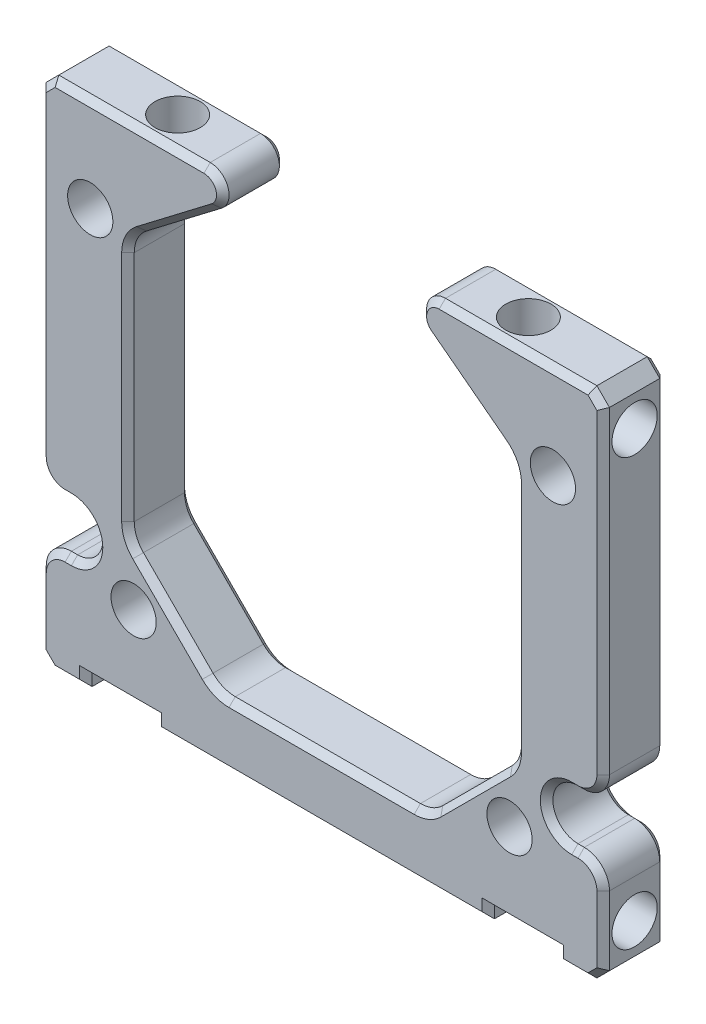
SolidWorks part; units mm, degrees
ref_plane "Front Plane" through (0, 0, 0) normal (0, 0, 1) x (1, 0, 0)
ref_plane "Top Plane" through (0, 0, 0) normal (0, 1, 0) x (1, 0, 0)
ref_plane "Right Plane" through (0, 0, 0) normal (1, 0, 0) x (0, 0, -1)
sketch "Sketch2" plane through (0, 0, 0) normal (0, 0, 1) x (1, 0, 0)
  line L0 (-22.4, 0) -> (22.4, 0) construction
  line L1 (-22.4, 20.4) -> (22.4, 20.4)
  line L2 (-22.4, 20.4) -> (-22.4, -20.4)
  line L3 (-22.4, -20.4) -> (22.4, -20.4)
  line L4 (22.4, 20.4) -> (22.4, -20.4)
  line L5 (0, 15.4) -> (0, -15.4) construction
  line L6 (-15.4, 15.4) -> (15.4, 15.4)
  line L7 (-15.4, 15.4) -> (-15.4, -15.4)
  line L8 (-15.4, -15.4) -> (15.4, -15.4)
  line L9 (15.4, 15.4) -> (15.4, -15.4)
  point P6 (0, 0)
  point P14 (0, 0)
  dimension "D1" = 44.8
  dimension "D2" = 40.8
  dimension "D3" = 5
  dimension "D4" = 7
extrude "Boss-Extrude1" add sketch "Sketch2" along normal blind 5
chamfer "Chamfer1" distance 1 angle 45 4 edges at (-22.4, -20.4, 2.5) (22.4, -20.4, 2.5) (22.4, 20.4, 2.5) (-22.4, 20.4, 2.5)
chamfer "Chamfer2" distance 7 angle 45 4 edges at (-15.4, -15.4, 2.5) (15.4, -15.4, 2.5) (15.4, 15.4, 2.5) (-15.4, 15.4, 2.5)
sketch "Sketch3" plane through (0, 0, 5) normal (0, 0, 1) x (1, 0, 0)
  line L0 (21.4, 20.4) -> (-21.4, 20.4) construction
  line L1 (22.4, -19.4) -> (22.4, 19.4) construction
  circle A0 centre (14.95, 12.95) radius 1.8
  dimension "D1" = 3.6
  dimension "D2" = 7.45
  dimension "D3" = 7.45
extrude "Cut-Extrude1" cut sketch "Sketch3" against normal through all
sketch "Sketch4" plane through (0, 20.4, 0) normal (0, 1, 0) x (1, 0, 0)
  line L0 (21.4, -5) -> (-21.4, -5) construction
  line L1 (22.4, 0) -> (22.4, -5) construction
  circle A0 centre (13.95, -2.5) radius 1.8
  dimension "D1" = 3.6
  dimension "D2" = 2.5
  dimension "D3" = 8.45
extrude "Cut-Extrude2" cut sketch "Sketch4" against normal blind 5
sketch "Sketch5" plane through (22.4, 0, 0) normal (1, 0, 0) x (0, 0, -1)
  line L0 (-5, -19.4) -> (-5, 19.4) construction
  line L1 (-5, 20.4) -> (0, 20.4) construction
  circle A0 centre (-2.5, 16.95) radius 1.8
  dimension "D2" = 3.6
  dimension "D3" = 3.45
  dimension "D1" = 2.5
extrude "Cut-Extrude3" cut sketch "Sketch5" against normal blind 5
mirror "Mirror1" about plane through (0, 0, 0) normal (0, 1, 0) of "Cut-Extrude3", "Cut-Extrude1"
mirror "Mirror2" about plane through (0, 0, 0) normal (1, 0, 0) of "Cut-Extrude2", "Mirror1", "Cut-Extrude1", "Cut-Extrude3"
sketch "Sketch8" plane through (0, 0, 5) normal (0, 0, 1) x (1, 0, 0)
  circle A0 centre (14.95, 12.95) radius 1.8
  circle A1 centre (-14.95, 12.95) radius 1.8
  circle A3 centre (-14.95, 12.95) radius 1.8 construction
  circle A4 centre (14.95, 12.95) radius 1.8 construction
extrude "Boss-Extrude2" add sketch "Sketch8" against normal up to surface (5 mm away) up to face at (16.75, -12.95, 0)
sketch "Sketch9" plane through (0, 0, 5) normal (0, 0, 1) x (1, 0, 0)
  line L0 (21.4, 20.4) -> (-21.4, 20.4) construction
  line L1 (22.4, -19.4) -> (22.4, 19.4) construction
  line L2 (-22.4, 19.4) -> (-22.4, -19.4) construction
  circle A0 centre (18.4, 12.95) radius 1.8
  circle A1 centre (-18.4, 12.95) radius 1.8
  dimension "D1" = 3.6
  dimension "D2" = 3.6
  dimension "D3" = 7.45
  dimension "D4" = 7.45
  dimension "D6" = 4
  dimension "D5" = 4
extrude "Cut-Extrude6" cut sketch "Sketch9" against normal through all
sketch "Sketch6" plane through (0, 0, 5) normal (0, 0, 1) x (1, 0, 0)
  line L0 (19.9, -9.9) -> (-19.9, -9.9) construction
  line L1 (22.4, -19.4) -> (22.4, 19.4) construction
  line L2 (-22.4, 19.4) -> (-22.4, -19.4) construction
  line L3 (-21.4, -20.4) -> (21.4, -20.4) construction
  line L4 (19.9, -11.9) -> (22.4, -11.9)
  line L5 (22.4, -11.9) -> (22.4, -7.9)
  line L6 (22.4, -7.9) -> (19.9, -7.9)
  line L7 (-19.9, -11.9) -> (-22.4, -11.9)
  line L8 (-22.4, -11.9) -> (-22.4, -7.9)
  line L9 (-22.4, -7.9) -> (-19.9, -7.9)
  circle A0 centre (19.9, -9.9) radius 2
  circle A1 centre (-19.9, -9.9) radius 2
  dimension "D1" = 4
  dimension "D2" = 4
  dimension "D4" = 2.5
  dimension "D3" = 2.5
  dimension "D5" = 10.5
extrude "Cut-Extrude4" cut sketch "Sketch6" against normal through all
fillet "Fillet2" radius 2 4 edges at (-22.4, -7.9, 2.5) (-22.4, -11.9, 2.5) (22.4, -7.9, 2.5) (22.4, -11.9, 2.5)
sketch "Sketch7" plane through (0, 0, 5) normal (0, 0, 1) x (1, 0, 0)
  line L0 (0, 0) -> (0, 7.8) construction
  line L1 (15.4, 8.4) -> (15.4, 12.4)
  line L2 (8.4, 15.4) -> (10.547, 15.4)
  line L3 (8.4, 15.4) -> (-8.4, 15.4) construction
  line L4 (-7.8873, 18.134) -> (-15.4, 12.4)
  line L5 (-8.4, 15.4) -> (-10.547, 15.4)
  line L6 (-15.4, 12.4) -> (-15.4, 8.4)
  line L7 (15.4, 12.4) -> (7.8873, 18.134)
  line L8 (8.4, 15.4) -> (15.4, 8.4)
  line L9 (8.4, 15.4) -> (15.4, 8.4) construction
  line L10 (-15.4, 8.4) -> (-8.4, 15.4) construction
  line L11 (-15.4, 8.4) -> (-8.4, 15.4)
  line L12 (15.4, -8.4) -> (15.4, 8.4) construction
  line L13 (-15.4, 8.4) -> (-15.4, -8.4) construction
  line L14 (-21.4, -20.4) -> (21.4, -20.4) construction
  circle A0 centre (0, 7.8) radius 13
  line M16 (-15.4, 8.4) -> (-8.4, 15.4)
  line M17 (-8.4, 15.4) -> (8.4, 15.4)
  line M18 (8.4, 15.4) -> (15.4, 8.4)
  dimension "D2" = 26
  dimension "D3" = 4
  dimension "D4" = 4
  dimension "D1" = 7.8
  dimension "D5" = 4.6
  dimension "D6" = 28.2
extrude "Cut-Extrude5" cut sketch "Sketch7" against normal through all contours A0 L1 L7 M17 M18 | A0 L4 L6 M16 M17 | A0 M17 | A0 L2 M18 | L5 A0 L11
sketch "Sketch10" plane through (0, 0, 5) normal (0, 0, 1) x (1, 0, 0)
  line L0 (-21.4, -20.4) -> (21.4, -20.4) construction
  line L1 (-18.75, -20.4) -> (-13.25, -20.4)
  line L2 (-18.75, -20.4) -> (-18.75, -19.45)
  line L3 (-18.75, -19.45) -> (-13.25, -19.45)
  line L4 (-13.25, -20.4) -> (-13.25, -19.45)
  line L5 (0, 0) -> (0, -28.5107) construction
  line L6 (13.25, -20.4) -> (18.75, -20.4)
  line L7 (13.25, -20.4) -> (13.25, -19.45)
  line L8 (13.25, -19.45) -> (18.75, -19.45)
  line L9 (18.75, -20.4) -> (18.75, -19.45)
  line L10 (-13.25, -20.4) -> (13.25, -20.4) construction
  point P13 (0, -20.4)
  dimension "D1" = 0.95
  dimension "D2" = 5.5
  dimension "D3" = 5.5
  dimension "D4" = 37.5
extrude "Cut-Extrude7" cut sketch "Sketch10" against normal through all
fillet "Fillet3" radius 2.5 6 edges at (-15.4, 12.4, 2.5) (15.4, 12.4, 2.5) (8.4, -15.4, 2.5) (-8.4, -15.4, 2.5) (-15.4, -8.4, 2.5) (15.4, -8.4, 2.5)
fillet "Fillet4" radius 1.5 2 edges at (-3.2, 20.4, 2.5) (3.2, 20.4, 2.5)
chamfer "Chamfer3" distance 0.5 angle 45 88 edges at (21.9, -19.9, 0) (20.075, -20.4, 0) (-20.075, -20.4, 0) (-21.9, -19.9, 0) (-22.4, -16.65, 0) (-22.4, 6.75, 0) (-21.9, 19.9, 0) (-15.378, 20.4, 0) (15.378, 20.4, 0) (21.9, 19.9, 0) (22.4, 6.75, 0) (22.4, -16.65, 0) (21.9, -19.9, 5) (-20.075, -20.4, 5) (20.075, -20.4, 5) (-21.9, -19.9, 5) (-22.4, 6.75, 5) (-22.4, -16.65, 5) (-21.9, 19.9, 5) (-15.378, 20.4, 5) (15.378, 20.4, 5) (21.9, 19.9, 5) (22.4, -16.65, 5) (22.4, 6.75, 5) (-21.8142, -12.4858, 5) (-20.15, -11.9, 5) (-17.9, -9.9, 5) (-20.15, -7.9, 5) (-21.8142, -7.3142, 5) (21.8142, -7.3142, 5) (20.15, -7.9, 5) (17.9, -9.9, 5) (20.15, -11.9, 5) (21.8142, -12.4858, 5) (-21.8142, -12.4858, 0) (-20.15, -11.9, 0) (-17.9, -9.9, 0) (-20.15, -7.9, 0) (-21.8142, -7.3142, 0) (21.8142, -7.3142, 0) (20.15, -7.9, 0) (17.9, -9.9, 0) (20.15, -11.9, 0) (21.8142, -12.4858, 0) (15.4, 1.8993, 0) (11.9, -11.9, 0) (0, -15.4, 0) (-11.9, -11.9, 0) (-15.4, 1.8993, 0) (11.9, -11.9, 5) (15.4, 1.8993, 5) (-15.4, 1.8993, 5) (-11.9, -11.9, 5) (0, -15.4, 5) (11.4313, 15.429, 5) (11.4313, 15.429, 0) (-11.4313, 15.429, 5) (-11.4313, 15.429, 0) (15.1408, 12.2717, 5) (-15.1408, 12.2717, 5) (15.1408, 12.2717, 0) (-15.1408, 12.2717, 0) (-15.2097, -8.3212, 5) (-8.3212, -15.2097, 5) (8.3212, -15.2097, 5) (15.2097, -8.3212, 5) (15.2097, -8.3212, 0) (8.3212, -15.2097, 0) (-8.3212, -15.2097, 0) (-15.2097, -8.3212, 0) (7.9349, 19.3803, 5) (-7.9349, 19.3803, 5) (7.9349, 19.3803, 0) (-7.9349, 19.3803, 0) (18.75, -19.925, 5) (16, -19.45, 5) (13.25, -19.925, 5) (0, -20.4, 5) (-13.25, -19.925, 5) (-16, -19.45, 5) (-18.75, -19.925, 5) (-18.75, -19.925, 0) (-16, -19.45, 0) (-13.25, -19.925, 0) (0, -20.4, 0) (13.25, -19.925, 0) (16, -19.45, 0) (18.75, -19.925, 0)
